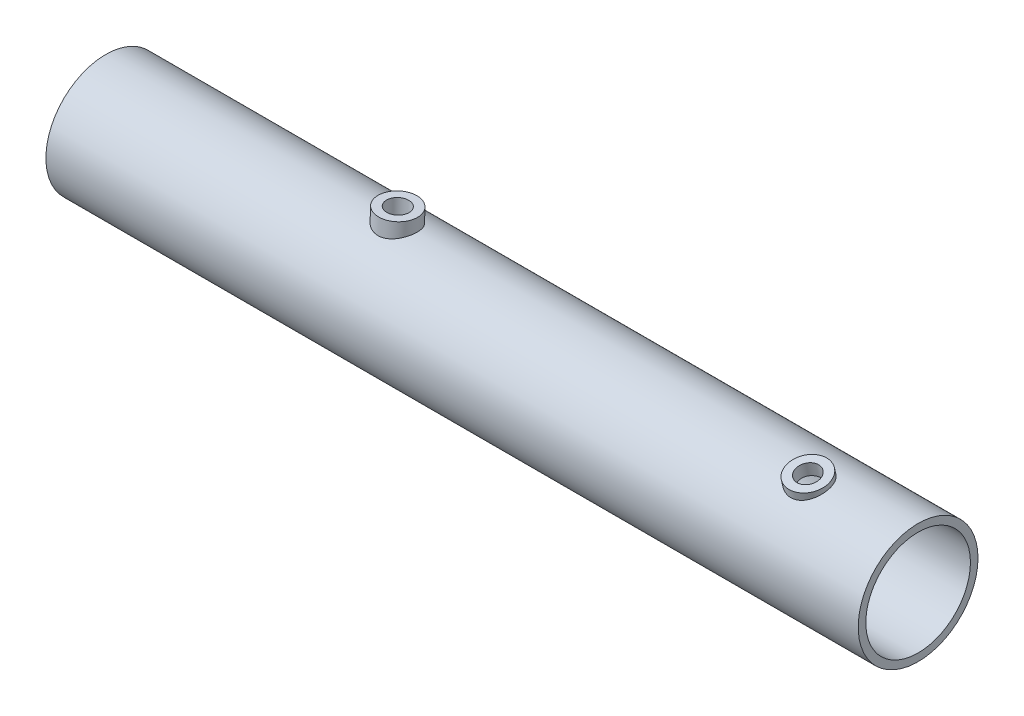
SolidWorks part; units mm, degrees
material "201 Annealed Stainless Steel (SS)"
ref_plane "Front Plane" through (0, 0, 0) normal (0, 0, 1) x (1, 0, 0)
ref_plane "Top Plane" through (0, 0, 0) normal (0, 1, 0) x (1, 0, 0)
ref_plane "Right Plane" through (0, 0, 0) normal (1, 0, 0) x (0, 0, -1)
sketch "Sketch1" plane through (0, 0, 0) normal (1, 0, 0) x (0, 0, -1)
  circle A0 centre (0, 0) radius 19
  circle A1 centre (0, 0) radius 21.75
extrude "Boss-Extrude1" add sketch "Sketch1" along normal blind 295
sketch "Sketch3" plane through (295, 0, 0) normal (1, 0, 0) x (0, 0, -1)
  circle A0 centre (0, 0) radius 19 construction
  circle A1 centre (0, 0) radius 19
sketch "Sketch4" plane through (0, 0, 0) normal (0, 0, 1) x (1, 0, 0)
  line L0 (295, 0) -> (0, 0) construction
sketch "Sketch5" plane through (0.0226, 23.1666, 5.2641) normal (-0.001, -0.9751, -0.2216) x (1, -0.0009, -0.0002)
  circle A0 centre (260.4367, 0.2915) radius 4 construction
  circle A1 centre (260.4367, 0.2915) radius 7
  circle A2 centre (260.4367, 0.2915) radius 7
  circle A3 centre (260.4367, 0.2915) radius 4
  dimension "D1" = 0
extrude "Boss-Extrude2" add sketch "Sketch5" along normal up to surface (2.0778 mm away)
sketch "Sketch6" plane through (0.1921, 27.1573, -0.6821) normal (-0.0071, -0.9997, 0.0251) x (1, -0.0071, 0.0002)
  circle A0 centre (105.2784, 0.0875) radius 4 construction
  circle A1 centre (105.2784, 0.0875) radius 7
  circle A2 centre (105.2784, 0.0875) radius 7
  circle A3 centre (105.2784, 0.0875) radius 4
  dimension "D1" = 0
extrude "Boss-Extrude3" add sketch "Sketch6" along normal up to surface (5.0265 mm away)
sketch "Sketch7" plane through (0.0226, 23.1666, 5.2641) normal (0.001, 0.9751, 0.2216) x (1, -0.0009, -0.0002)
  circle A0 centre (260.4367, -0.2915) radius 4 construction
  circle A1 centre (260.4367, -0.2915) radius 4
extrude "Cut-Extrude1" cut sketch "Sketch7" against normal blind 10
sketch "Sketch8" plane through (0.1921, 27.1573, -0.6821) normal (0.0071, 0.9997, -0.0251) x (1, -0.0071, 0.0002)
  circle A0 centre (105.2784, -0.0875) radius 4 construction
  circle A1 centre (105.2784, -0.0875) radius 4
extrude "Cut-Extrude2" cut sketch "Sketch8" against normal blind 20
